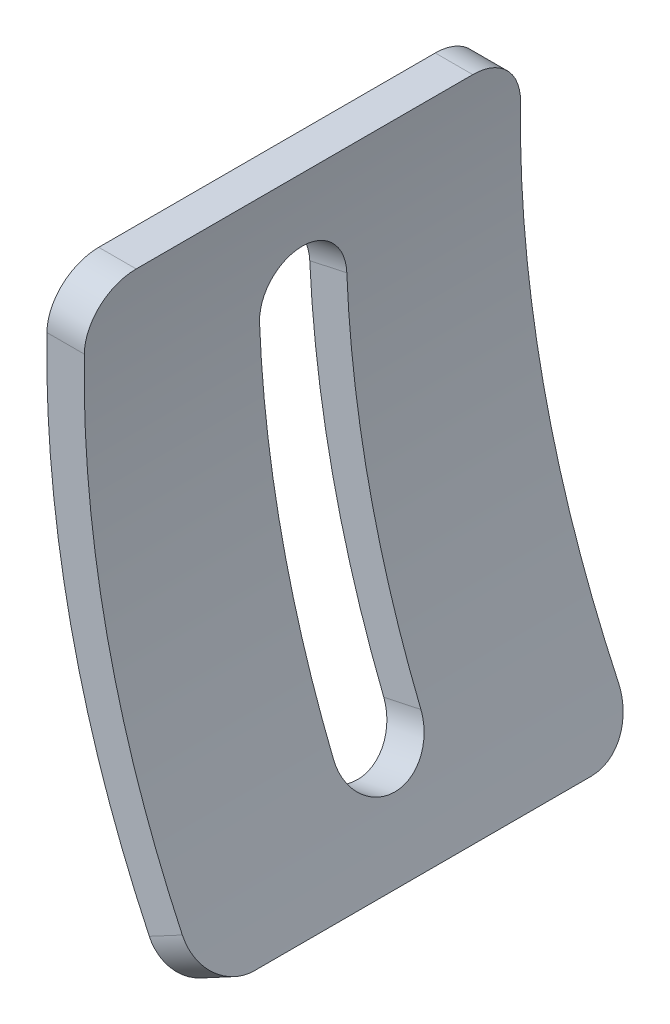
SolidWorks part; units mm, degrees
ref_plane "Plan de face" through (0, 0, 0) normal (0, 0, 1) x (1, 0, 0)
ref_plane "Plan de dessus" through (0, 0, 0) normal (0, 1, 0) x (1, 0, 0)
ref_plane "Plan de droite" through (0, 0, 0) normal (1, 0, 0) x (0, 0, -1)
sketch "Esquisse1" plane through (0, 0, 0) normal (0, 0, 1) x (1, 0, 0)
  line L1 (0, 0) -> (-3.0062, 0)
  line L2 (9.5, -44) -> (6.854, -45.4137)
  arc A0 (-3.0062, 0) -> (6.854, -45.4137) centre (81.8247, -5.3589) ccw
  arc A1 (0, 0) -> (9.5, -44) centre (81.8247, -5.3589) ccw
  dimension "D1" = 3
  dimension "D2" = 82
  dimension "D4" = 9.5
  dimension "D3" = 44
extrude "Extrusion1" add sketch "Esquisse1" along normal mid plane 35
fillet "Congé1" radius 4 4 edges at (-1.5031, 0, 17.5) (-1.5031, 0, -17.5) (8.177, -44.7068, -17.5) (8.177, -44.7068, 17.5)
ref_plane "Plan1" through (0, 0, 0) normal (-0.9775, -0.211, 0) x (0, 0, 1)
sketch "Esquisse2" plane through (0, 0, 0) normal (-0.9775, -0.211, 0) x (0, 0, 1)
  line L0 (0, 0) -> (0, -50.7273) construction
  line L1 (-20.2487, -22.6014) -> (24.2093, -22.6014) construction
  line L2 (13.5, 0.6344) -> (-13.5, 0.6344) construction
  line L3 (-3.5, -36.6014) -> (-3.5, -8.6014)
  line L4 (13.5, -45.8373) -> (-13.5, -45.8373) construction
  line L5 (3.5, -36.6014) -> (3.5, -8.6014)
  arc A0 (-3.5, -8.6014) -> (3.5, -8.6014) centre (0, -8.6014) cw
  arc A1 (3.5, -36.6014) -> (-3.5, -36.6014) centre (0, -36.6014) cw
  dimension "D2" = 35
  dimension "D1" = 7
extrude "Enlèv. mat.-Extru.1" cut sketch "Esquisse2" along normal blind 35
